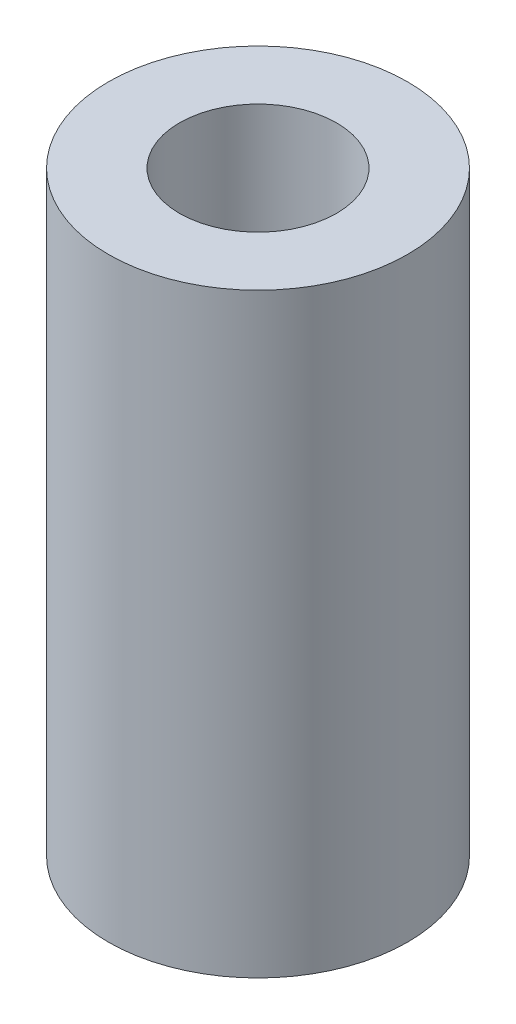
SolidWorks part; units mm, degrees
ref_plane "Front Plane" through (0, 0, 0) normal (0, 0, 1) x (1, 0, 0)
ref_plane "Top Plane" through (0, 0, 0) normal (0, 1, 0) x (1, 0, 0)
ref_plane "Right Plane" through (0, 0, 0) normal (1, 0, 0) x (0, 0, -1)
sketch "Sketch1" plane through (0, 0, 0) normal (0, 1, 0) x (1, 0, 0)
  circle A0 centre (0, 0) radius 2
  circle A1 centre (0, 0) radius 3.81
  dimension "D1" = 4
  dimension "D2" = 7.62
extrude "Boss-Extrude1" add sketch "Sketch1" along normal blind 15.175
